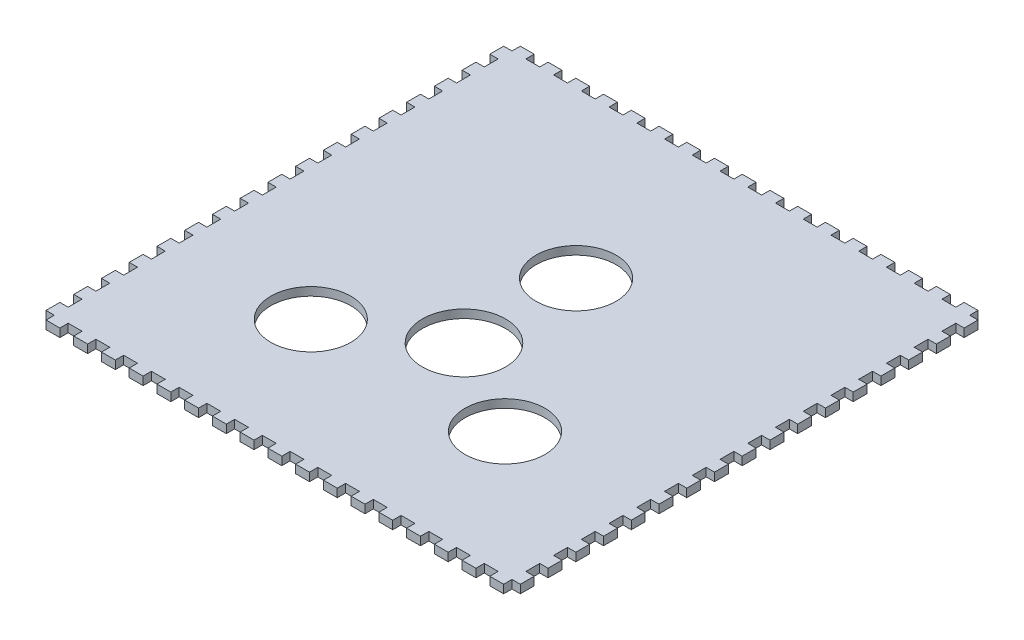
SolidWorks part; units mm, degrees
ref_plane "Спереди" through (0, 0, 0) normal (0, 0, 1) x (1, 0, 0)
ref_plane "Сверху" through (0, 0, 0) normal (0, 1, 0) x (1, 0, 0)
ref_plane "Справа" through (0, 0, 0) normal (1, 0, 0) x (0, 0, -1)
sketch "Эскиз1" plane through (0, 0, 0) normal (0, 1, 0) x (1, 0, 0)
  line L0 (0, 165) -> (0, 168)
  line L1 (5, 0) -> (10, 0)
  line L2 (0, 5) -> (0, 10)
  line L3 (5, 165) -> (10, 165)
  line L4 (165, 5) -> (165, 10)
  line L5 (0, 168) -> (5, 168)
  line L6 (5, 168) -> (5, 165)
  line L7 (10, 165) -> (10, 168)
  line L8 (10, 168) -> (15, 168)
  line L9 (15, 168) -> (15, 165)
  line L10 (20, 165) -> (20, 168)
  line L11 (20, 168) -> (25, 168)
  line L12 (25, 168) -> (25, 165)
  line L13 (30, 165) -> (30, 168)
  line L14 (30, 168) -> (35, 168)
  line L15 (35, 168) -> (35, 165)
  line L16 (40, 165) -> (40, 168)
  line L17 (40, 168) -> (45, 168)
  line L18 (45, 168) -> (45, 165)
  line L19 (50, 165) -> (50, 168)
  line L20 (50, 168) -> (55, 168)
  line L21 (55, 168) -> (55, 165)
  line L22 (60, 165) -> (60, 168)
  line L23 (60, 168) -> (65, 168)
  line L24 (65, 168) -> (65, 165)
  line L25 (70, 165) -> (70, 168)
  line L26 (70, 168) -> (75, 168)
  line L27 (75, 168) -> (75, 165)
  line L28 (80, 165) -> (80, 168)
  line L29 (80, 168) -> (85, 168)
  line L30 (85, 168) -> (85, 165)
  line L31 (90, 165) -> (90, 168)
  line L32 (90, 168) -> (95, 168)
  line L33 (95, 168) -> (95, 165)
  line L34 (100, 165) -> (100, 168)
  line L35 (100, 168) -> (105, 168)
  line L36 (105, 168) -> (105, 165)
  line L37 (110, 165) -> (110, 168)
  line L38 (110, 168) -> (115, 168)
  line L39 (115, 168) -> (115, 165)
  line L40 (120, 165) -> (120, 168)
  line L41 (120, 168) -> (125, 168)
  line L42 (125, 168) -> (125, 165)
  line L43 (130, 165) -> (130, 168)
  line L44 (130, 168) -> (135, 168)
  line L45 (135, 168) -> (135, 165)
  line L46 (140, 165) -> (140, 168)
  line L47 (140, 168) -> (145, 168)
  line L48 (145, 168) -> (145, 165)
  line L49 (150, 165) -> (150, 168)
  line L50 (150, 168) -> (155, 168)
  line L51 (155, 168) -> (155, 165)
  line L52 (160, 165) -> (160, 168)
  line L53 (160, 168) -> (165, 168)
  line L54 (165, 168) -> (165, 165)
  line L55 (15, 165) -> (20, 165)
  line L56 (25, 165) -> (30, 165)
  line L57 (35, 165) -> (40, 165)
  line L58 (45, 165) -> (50, 165)
  line L59 (55, 165) -> (60, 165)
  line L60 (65, 165) -> (70, 165)
  line L61 (75, 165) -> (80, 165)
  line L62 (85, 165) -> (90, 165)
  line L63 (95, 165) -> (100, 165)
  line L64 (105, 165) -> (110, 165)
  line L65 (115, 165) -> (120, 165)
  line L66 (125, 165) -> (130, 165)
  line L67 (135, 165) -> (140, 165)
  line L68 (145, 165) -> (150, 165)
  line L69 (155, 165) -> (160, 165)
  line L70 (0, 82.5) -> (165, 82.5) construction
  line L71 (155, 0) -> (160, 0)
  line L72 (145, 0) -> (150, 0)
  line L73 (135, 0) -> (140, 0)
  line L74 (125, 0) -> (130, 0)
  line L75 (115, 0) -> (120, 0)
  line L76 (105, 0) -> (110, 0)
  line L77 (95, 0) -> (100, 0)
  line L78 (85, 0) -> (90, 0)
  line L79 (75, 0) -> (80, 0)
  line L80 (65, 0) -> (70, 0)
  line L81 (55, 0) -> (60, 0)
  line L82 (45, 0) -> (50, 0)
  line L83 (35, 0) -> (40, 0)
  line L84 (25, 0) -> (30, 0)
  line L85 (15, 0) -> (20, 0)
  line L86 (165, -3) -> (165, 0)
  line L87 (160, -3) -> (165, -3)
  line L88 (160, 0) -> (160, -3)
  line L89 (155, -3) -> (155, 0)
  line L90 (150, -3) -> (155, -3)
  line L91 (150, 0) -> (150, -3)
  line L92 (145, -3) -> (145, 0)
  line L93 (140, -3) -> (145, -3)
  line L94 (140, 0) -> (140, -3)
  line L95 (135, -3) -> (135, 0)
  line L96 (130, -3) -> (135, -3)
  line L97 (130, 0) -> (130, -3)
  line L98 (125, -3) -> (125, 0)
  line L99 (120, -3) -> (125, -3)
  line L100 (120, 0) -> (120, -3)
  line L101 (115, -3) -> (115, 0)
  line L102 (110, -3) -> (115, -3)
  line L103 (110, 0) -> (110, -3)
  line L104 (105, -3) -> (105, 0)
  line L105 (100, -3) -> (105, -3)
  line L106 (100, 0) -> (100, -3)
  line L107 (95, -3) -> (95, 0)
  line L108 (90, -3) -> (95, -3)
  line L109 (90, 0) -> (90, -3)
  line L110 (85, -3) -> (85, 0)
  line L111 (80, -3) -> (85, -3)
  line L112 (80, 0) -> (80, -3)
  line L113 (75, -3) -> (75, 0)
  line L114 (70, -3) -> (75, -3)
  line L115 (70, 0) -> (70, -3)
  line L116 (65, -3) -> (65, 0)
  line L117 (60, -3) -> (65, -3)
  line L118 (60, 0) -> (60, -3)
  line L119 (55, -3) -> (55, 0)
  line L120 (50, -3) -> (55, -3)
  line L121 (50, 0) -> (50, -3)
  line L122 (45, -3) -> (45, 0)
  line L123 (40, -3) -> (45, -3)
  line L124 (40, 0) -> (40, -3)
  line L125 (35, -3) -> (35, 0)
  line L126 (30, -3) -> (35, -3)
  line L127 (30, 0) -> (30, -3)
  line L128 (25, -3) -> (25, 0)
  line L129 (20, -3) -> (25, -3)
  line L130 (20, 0) -> (20, -3)
  line L131 (15, -3) -> (15, 0)
  line L132 (10, -3) -> (15, -3)
  line L133 (10, 0) -> (10, -3)
  line L134 (5, -3) -> (5, 0)
  line L135 (0, -3) -> (5, -3)
  line L136 (5, 0) -> (10, 0)
  line L137 (0, 0) -> (0, -3)
  line L138 (155, 0) -> (160, 0)
  line L139 (145, 0) -> (150, 0)
  line L140 (135, 0) -> (140, 0)
  line L141 (125, 0) -> (130, 0)
  line L142 (115, 0) -> (120, 0)
  line L143 (105, 0) -> (110, 0)
  line L144 (95, 0) -> (100, 0)
  line L145 (85, 0) -> (90, 0)
  line L146 (75, 0) -> (80, 0)
  line L147 (65, 0) -> (70, 0)
  line L148 (55, 0) -> (60, 0)
  line L149 (45, 0) -> (50, 0)
  line L150 (35, 0) -> (40, 0)
  line L151 (25, 0) -> (30, 0)
  line L152 (15, 0) -> (20, 0)
  line L153 (165, 165) -> (168, 165)
  line L154 (168, 165) -> (168, 160)
  line L155 (168, 160) -> (165, 160)
  line L156 (165, 155) -> (168, 155)
  line L157 (168, 155) -> (168, 150)
  line L158 (168, 150) -> (165, 150)
  line L159 (165, 145) -> (168, 145)
  line L160 (168, 145) -> (168, 140)
  line L161 (168, 140) -> (165, 140)
  line L162 (165, 135) -> (168, 135)
  line L163 (168, 135) -> (168, 130)
  line L164 (168, 130) -> (165, 130)
  line L165 (165, 125) -> (168, 125)
  line L166 (168, 125) -> (168, 120)
  line L167 (168, 120) -> (165, 120)
  line L168 (165, 115) -> (168, 115)
  line L169 (168, 115) -> (168, 110)
  line L170 (168, 110) -> (165, 110)
  line L171 (165, 105) -> (168, 105)
  line L172 (168, 105) -> (168, 100)
  line L173 (168, 100) -> (165, 100)
  line L174 (165, 95) -> (168, 95)
  line L175 (168, 95) -> (168, 90)
  line L176 (168, 90) -> (165, 90)
  line L177 (165, 85) -> (168, 85)
  line L178 (168, 85) -> (168, 80)
  line L179 (168, 80) -> (165, 80)
  line L180 (165, 75) -> (168, 75)
  line L181 (168, 75) -> (168, 70)
  line L182 (168, 70) -> (165, 70)
  line L183 (165, 65) -> (168, 65)
  line L184 (168, 65) -> (168, 60)
  line L185 (168, 60) -> (165, 60)
  line L186 (165, 55) -> (168, 55)
  line L187 (168, 55) -> (168, 50)
  line L188 (168, 50) -> (165, 50)
  line L189 (165, 45) -> (168, 45)
  line L190 (168, 45) -> (168, 40)
  line L191 (168, 40) -> (165, 40)
  line L192 (165, 35) -> (168, 35)
  line L193 (168, 35) -> (168, 30)
  line L194 (168, 30) -> (165, 30)
  line L195 (165, 25) -> (168, 25)
  line L196 (168, 25) -> (168, 20)
  line L197 (168, 20) -> (165, 20)
  line L198 (165, 15) -> (168, 15)
  line L199 (168, 15) -> (168, 10)
  line L200 (168, 10) -> (165, 10)
  line L201 (165, 5) -> (168, 5)
  line L202 (168, 5) -> (168, 0)
  line L203 (168, 0) -> (165, 0)
  line L204 (82.5, -3) -> (82.5, 168) construction
  line L205 (-3, 5) -> (-3, 0)
  line L206 (-3, 0) -> (0, 0)
  line L207 (0, 5) -> (-3, 5)
  line L208 (-3, 10) -> (0, 10)
  line L209 (-3, 15) -> (-3, 10)
  line L210 (0, 15) -> (-3, 15)
  line L211 (-3, 20) -> (0, 20)
  line L212 (-3, 25) -> (-3, 20)
  line L213 (0, 25) -> (-3, 25)
  line L214 (-3, 30) -> (0, 30)
  line L215 (-3, 35) -> (-3, 30)
  line L216 (0, 35) -> (-3, 35)
  line L217 (-3, 40) -> (0, 40)
  line L218 (-3, 45) -> (-3, 40)
  line L219 (0, 45) -> (-3, 45)
  line L220 (-3, 50) -> (0, 50)
  line L221 (-3, 55) -> (-3, 50)
  line L222 (0, 55) -> (-3, 55)
  line L223 (-3, 60) -> (0, 60)
  line L224 (-3, 65) -> (-3, 60)
  line L225 (0, 65) -> (-3, 65)
  line L226 (-3, 70) -> (0, 70)
  line L227 (-3, 75) -> (-3, 70)
  line L228 (0, 75) -> (-3, 75)
  line L229 (-3, 80) -> (0, 80)
  line L230 (-3, 85) -> (-3, 80)
  line L231 (0, 85) -> (-3, 85)
  line L232 (-3, 90) -> (0, 90)
  line L233 (-3, 95) -> (-3, 90)
  line L234 (0, 95) -> (-3, 95)
  line L235 (-3, 100) -> (0, 100)
  line L236 (-3, 105) -> (-3, 100)
  line L237 (0, 105) -> (-3, 105)
  line L238 (-3, 110) -> (0, 110)
  line L239 (-3, 115) -> (-3, 110)
  line L240 (0, 115) -> (-3, 115)
  line L241 (-3, 120) -> (0, 120)
  line L242 (-3, 125) -> (-3, 120)
  line L243 (0, 125) -> (-3, 125)
  line L244 (-3, 130) -> (0, 130)
  line L245 (-3, 135) -> (-3, 130)
  line L246 (0, 135) -> (-3, 135)
  line L247 (-3, 140) -> (0, 140)
  line L248 (-3, 145) -> (-3, 140)
  line L249 (0, 145) -> (-3, 145)
  line L250 (-3, 150) -> (0, 150)
  line L251 (-3, 155) -> (-3, 150)
  line L252 (0, 155) -> (-3, 155)
  line L253 (-3, 160) -> (0, 160)
  line L254 (-3, 165) -> (-3, 160)
  line L255 (0, 165) -> (-3, 165)
  line L256 (165, 155) -> (165, 160)
  line L257 (165, 145) -> (165, 150)
  line L258 (165, 135) -> (165, 140)
  line L259 (165, 125) -> (165, 130)
  line L260 (165, 115) -> (165, 120)
  line L261 (165, 105) -> (165, 110)
  line L262 (165, 95) -> (165, 100)
  line L263 (165, 85) -> (165, 90)
  line L264 (165, 75) -> (165, 80)
  line L265 (165, 65) -> (165, 70)
  line L266 (165, 55) -> (165, 60)
  line L267 (165, 45) -> (165, 50)
  line L268 (165, 35) -> (165, 40)
  line L269 (165, 25) -> (165, 30)
  line L270 (0, 15) -> (0, 20)
  line L271 (0, 25) -> (0, 30)
  line L272 (0, 35) -> (0, 40)
  line L273 (0, 45) -> (0, 50)
  line L274 (0, 55) -> (0, 60)
  line L275 (0, 65) -> (0, 70)
  line L276 (0, 75) -> (0, 80)
  line L277 (0, 155) -> (0, 160)
  line L278 (0, 145) -> (0, 150)
  line L279 (0, 135) -> (0, 140)
  line L280 (0, 125) -> (0, 130)
  line L281 (0, 115) -> (0, 120)
  line L282 (0, 105) -> (0, 110)
  line L283 (0, 95) -> (0, 100)
  line L284 (0, 85) -> (0, 90)
  line L285 (165, 15) -> (165, 20)
  line L286 (82.5, 168) -> (82.5, 134.4615) construction
  line L287 (82.5, 134.4615) -> (22.5, 30.5385) construction
  line L288 (22.5, 30.5385) -> (142.5, 30.5385) construction
  line L289 (142.5, 30.5385) -> (82.5, 134.4615) construction
  line L290 (82.5, 30.5385) -> (82.5, -3) construction
  line L291 (142.5, 30.5385) -> (52.5, 82.5) construction
  circle A0 centre (82.5, 65.1795) radius 34.641 construction
  circle A1 centre (47.5, 44.9722) radius 14.4338
  circle A2 centre (117.5, 44.9722) radius 14.4338
  circle A3 centre (82.5, 105.594) radius 14.4338
  circle A4 centre (82.5, 65.1795) radius 15
  point P4 (12.5, 168)
  point P73 (2.5, 168)
  dimension "D10" = 35
  dimension "D12" = 35
  dimension "D13" = 30
  dimension "D1" = 165
  dimension "D2" = 5
  dimension "D3" = 3
  dimension "D4" = 5
  dimension "D6" = 10
  dimension "D7" = 3
  dimension "D8" = 17
  dimension "D9" = 120
  dimension "D11" = 35
  dimension "D5" = 17
extrude "Бобышка-Вытянуть2" add sketch "Эскиз1" along normal blind 3 contours L198 L285 L197 L196 L195 L269 L194 L193 L192 L268 L191 L190 L189 L267 L188 L187 L186 L266 L185 L184 L183 L265 L182 L181 L180 L264 L179 L178 L177 L263 L176 L175 L174 L262 L173 L172 L171 L261 L170 L169 L168 L260 L167 L166 L165 L259 L164 L163 L162 L258 L161
